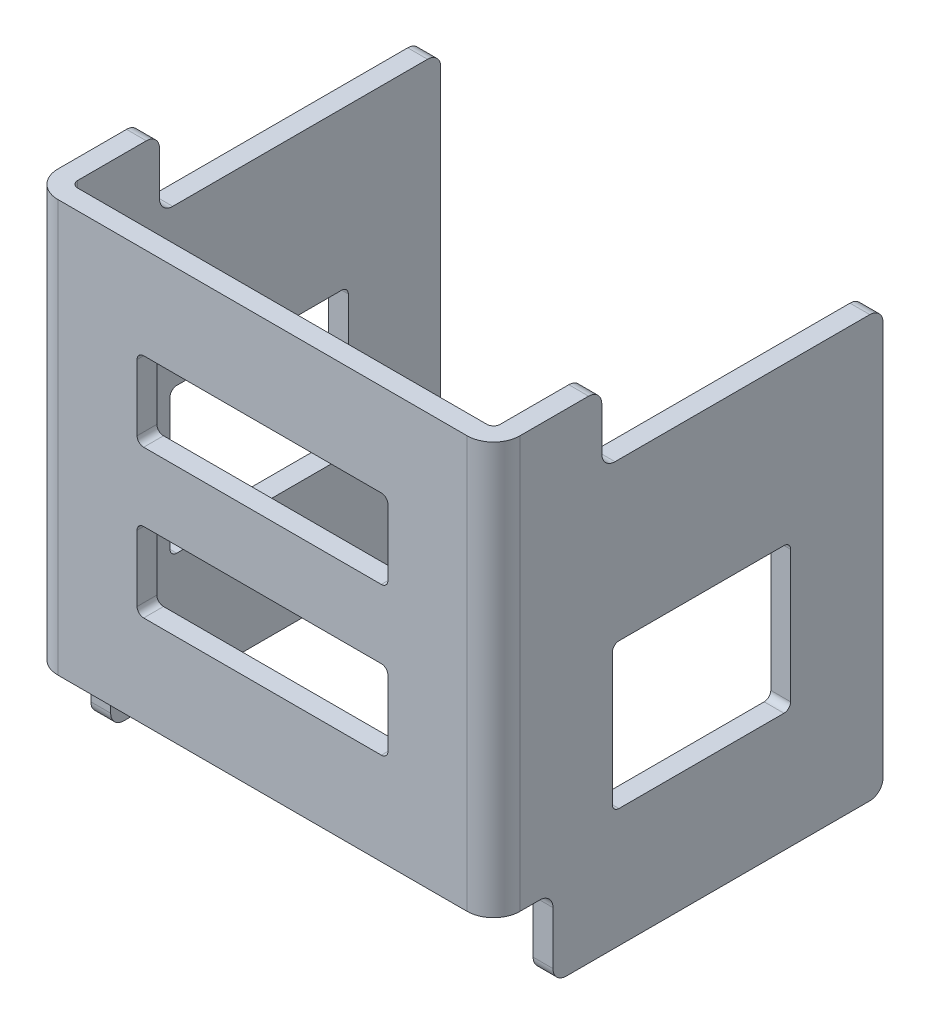
SolidWorks part; units mm, degrees
ref_plane "Front Plane" through (0, 0, 0) normal (0, 0, 1) x (1, 0, 0)
ref_plane "Top Plane" through (0, 0, 0) normal (0, 1, 0) x (1, 0, 0)
ref_plane "Right Plane" through (0, 0, 0) normal (1, 0, 0) x (0, 0, -1)
ref_plane "Plane1" through (16, 0, 0) normal (-1, 0, 0) x (0, -1, 0)
sketch "Sketch1" plane through (16, 0, 0) normal (-1, 0, 0) x (0, -1, 0)
  line L0 (27.5, 18.5) -> (27.5, -11)
  line L1 (27.5, -11) -> (64.7, -11)
  line L2 (64.7, -11) -> (64.7, 18.5)
  line L3 (64.7, 18.5) -> (27.5, 18.5)
extrude "Boss-Extrude1" add sketch "Sketch1" against normal blind 1.5
sketch "Sketch2" plane through (17.5, 0, 0) normal (1, 0, 0) x (0, 0, -1)
  line L0 (-18.5, -64.7) -> (-14, -64.7)
  line L1 (-14, -64.7) -> (-14, -58.7)
  line L2 (-14, -58.7) -> (-18.5, -58.7)
  line L3 (-18.5, -58.7) -> (-18.5, -64.7)
extrude "Cut-Extrude1" cut sketch "Sketch2" against normal through all
sketch "Sketch3" plane through (16, 0, 0) normal (-1, 0, 0) x (0, 0, 1)
  line L0 (17, -27.5) -> (18.5, -27.5)
  line L1 (18.5, -27.5) -> (18.5, -58.7)
  line L2 (18.5, -58.7) -> (17, -58.7)
  line L3 (17, -58.7) -> (17, -27.5)
extrude "Boss-Extrude2" add sketch "Sketch3" along normal blind 33.5
sketch "Sketch4" plane through (0, 0, 17) normal (0, 0, -1) x (-1, 0, 0)
  line L0 (17.5, -58.7) -> (16, -58.7)
  line L1 (16, -58.7) -> (16, -27.5)
  line L2 (16, -27.5) -> (17.5, -27.5)
  line L3 (17.5, -27.5) -> (17.5, -58.7)
extrude "Boss-Extrude3" add sketch "Sketch4" along normal blind 28
sketch "Sketch5" plane through (0, -58.7, 0) normal (0, -1, 0) x (1, 0, 0)
  line L0 (-17.5, 14) -> (-16, 14)
  line L1 (-16, 14) -> (-16, -11)
  line L2 (-16, -11) -> (-17.5, -11)
  line L3 (-17.5, -11) -> (-17.5, 14)
extrude "Boss-Extrude4" add sketch "Sketch5" along normal blind 6
sketch "Sketch6" plane through (17.5, 0, 0) normal (1, 0, 0) x (0, 0, -1)
  line L0 (11, -27.5) -> (-10.3, -27.5)
  line L1 (-10.3, -27.5) -> (-10.3, -32.8)
  line L2 (-10.3, -32.8) -> (11, -32.8)
  line L3 (11, -32.8) -> (11, -27.5)
extrude "Cut-Extrude2" cut sketch "Sketch6" against normal up to next
sketch "Sketch7" plane through (-17.5, 0, 0) normal (-1, 0, 0) x (0, 0, 1)
  line L0 (-11, -27.5) -> (-11, -32.8)
  line L1 (-11, -32.8) -> (10.3, -32.8)
  line L2 (10.3, -32.8) -> (10.3, -27.5)
  line L3 (10.3, -27.5) -> (-11, -27.5)
extrude "Cut-Extrude3" cut sketch "Sketch7" against normal through all
fillet "Fillet1" radius 0.5 2 edges at (-16, -43.1, 17) (16, -43.1, 17)
fillet "Fillet2" radius 2 2 edges at (17.5, -43.1, 18.5) (-17.5, -43.1, 18.5)
sketch "Sketch8" plane through (0, 0, 18.5) normal (0, 0, 1) x (1, 0, 0)
  line L0 (0, -27.5) -> (0, -58.7) construction
  line L1 (15.5, -27.5) -> (-15.5, -27.5) construction
  line L2 (-15.5, -58.7) -> (15.5, -58.7) construction
  line L3 (9.5, -34.5) -> (-9.5, -34.5)
  line L4 (-15.5, -27.5) -> (-15.5, -58.7) construction
  line L5 (-15.5, -43.1) -> (15.5, -43.1) construction
  line L6 (15.5, -58.7) -> (15.5, -27.5) construction
  line L7 (-9.5, -34.5) -> (-9.5, -40.5)
  line L8 (-9.5, -40.5) -> (9.5, -40.5)
  line L9 (9.5, -34.5) -> (9.5, -40.5)
  line L10 (9.5, -51.7) -> (9.5, -45.7)
  line L11 (-9.5, -45.7) -> (9.5, -45.7)
  line L12 (-9.5, -51.7) -> (-9.5, -45.7)
  line L13 (9.5, -51.7) -> (-9.5, -51.7)
  point P17 (0, -40.5)
  point P18 (0, -34.5)
  dimension "D1" = 7
  dimension "D2" = 6
  dimension "D3" = 9.5
extrude "Cut-Extrude4" cut sketch "Sketch8" against normal blind 1.5
fillet "Fillet3" radius 0.5 8 edges at (-9.5, -45.7, 17.75) (9.5, -45.7, 17.75) (9.5, -51.7, 17.75) (-9.5, -51.7, 17.75) (9.5, -34.5, 17.75) (9.5, -40.5, 17.75) (-9.5, -34.5, 17.75) (-9.5, -40.5, 17.75)
sketch "Sketch9" plane through (17.5, 0, 0) normal (1, 0, 0) x (0, 0, -1)
  line L0 (11, -32.8) -> (11, -64.7) construction
  line L1 (-9.5, -44.7) -> (4, -44.7)
  line L2 (-9.5, -44.7) -> (-9.5, -55.7)
  line L3 (-9.5, -55.7) -> (4, -55.7)
  line L4 (4, -44.7) -> (4, -55.7)
  line L5 (11, -64.7) -> (-14, -64.7) construction
  dimension "D1" = 7
  dimension "D2" = 13.5
  dimension "D3" = 11
  dimension "D4" = 9
extrude "Cut-Extrude5" cut sketch "Sketch9" against normal blind 35
fillet "Fillet4" radius 0.5 8 edges at (-16.75, -55.7, 9.5) (16.75, -55.7, -4) (-16.75, -55.7, -4) (16.75, -44.7, -4) (-16.75, -44.7, -4) (16.75, -44.7, 9.5) (-16.75, -44.7, 9.5) (16.75, -55.7, 9.5)
fillet "Fillet5" radius 1 12 edges at (16.75, -64.7, -11) (16.75, -64.7, 14) (16.75, -58.7, 14) (-16.75, -58.7, 14) (-16.75, -64.7, 14) (-16.75, -64.7, -11) (-16.75, -32.8, -11) (-16.75, -32.8, 10.3) (-16.75, -27.5, 10.3) (16.75, -27.5, 10.3) (16.75, -32.8, 10.3) (16.75, -32.8, -11)
